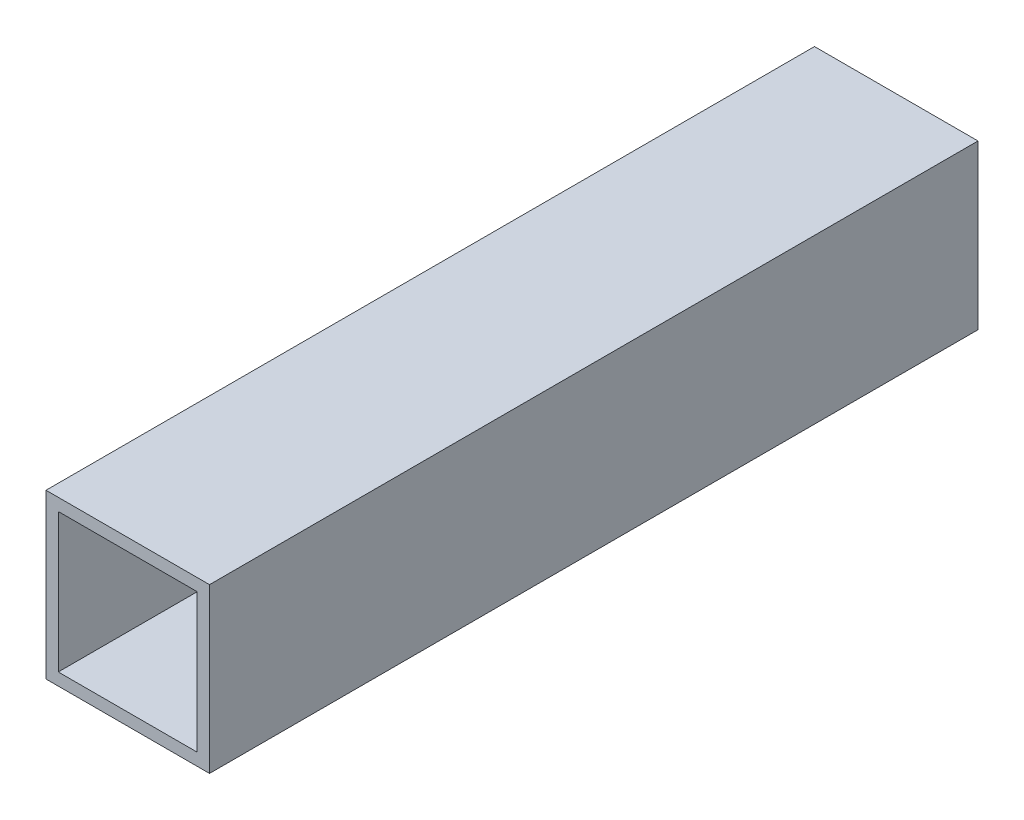
SolidWorks part; units mm, degrees
material "Hexcel AS4C (3000 Filaments)"
ref_plane "Front Plane" through (0, 0, 0) normal (0, 0, 1) x (1, 0, 0)
ref_plane "Top Plane" through (0, 0, 0) normal (0, 1, 0) x (1, 0, 0)
ref_plane "Right Plane" through (0, 0, 0) normal (1, 0, 0) x (0, 0, -1)
sketch "Sketch1" plane through (0, 0, 0) normal (0, 0, 1) x (1, 0, 0)
  line L0 (-6.666, 7.0227) -> (10.334, 7.0227)
  line L1 (-8.166, 8.5227) -> (11.834, 8.5227)
  line L2 (-8.166, 8.5227) -> (-8.166, -11.4773)
  line L3 (-8.166, -11.4773) -> (11.834, -11.4773)
  line L4 (11.834, 8.5227) -> (11.834, -11.4773)
  line L5 (10.334, 7.0227) -> (10.334, -9.9773)
  line L6 (-6.666, -9.9773) -> (10.334, -9.9773)
  line L7 (-6.666, 7.0227) -> (-6.666, -9.9773)
  dimension "D1" = 20
  dimension "D2" = 20
  dimension "D3" = 1.5
extrude "Boss-Extrude1" add sketch "Sketch1" along normal blind 94
